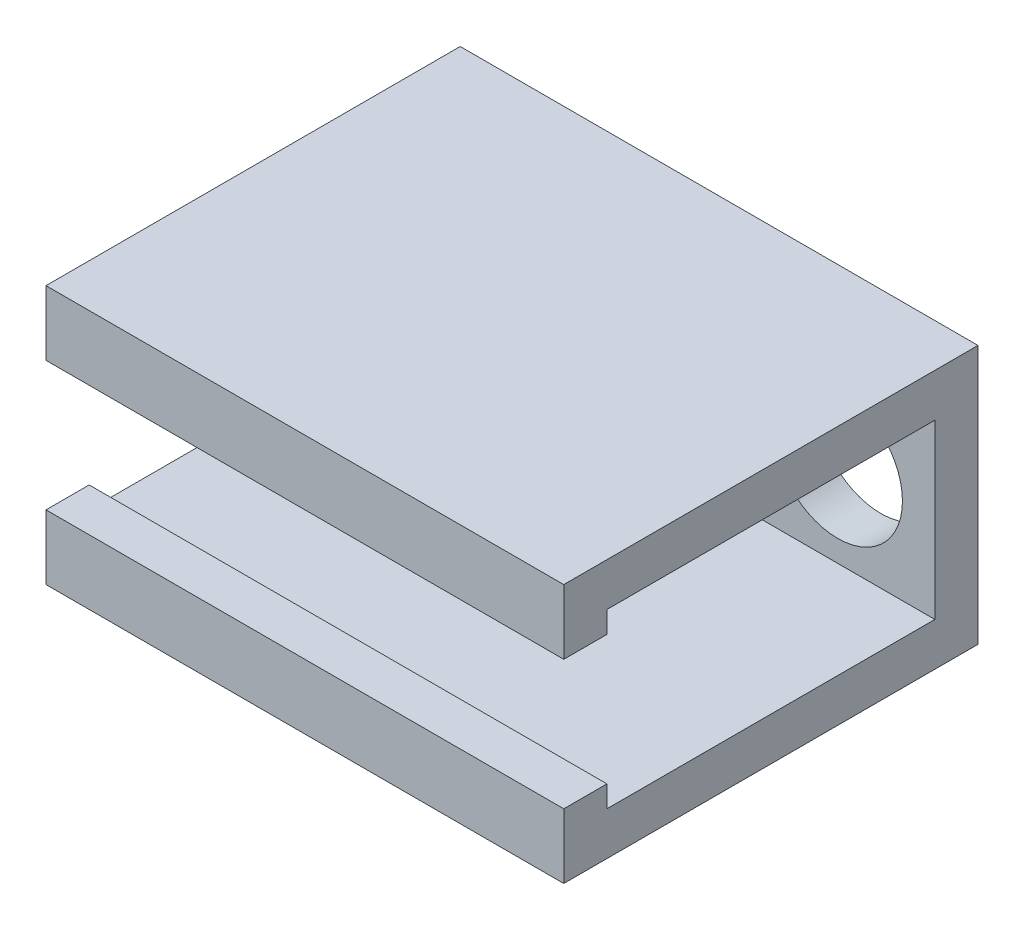
SolidWorks part; units mm, degrees
ref_plane "Front Plane" through (0, 0, 0) normal (0, 0, 1) x (1, 0, 0)
ref_plane "Top Plane" through (0, 0, 0) normal (0, 1, 0) x (1, 0, 0)
ref_plane "Right Plane" through (0, 0, 0) normal (1, 0, 0) x (0, 0, -1)
sketch "Sketch1" plane through (0, 0, 0) normal (1, 0, 0) x (0, 0, -1)
  line L0 (0, 7.5) -> (-5, 7.5)
  line L1 (-5, 7.5) -> (-5, 15)
  line L2 (-5, 15) -> (43, 15)
  line L3 (43, 15) -> (43, -15)
  line L9 (38, -10) -> (38, 10)
  line L11 (0, 7.5) -> (0, 10)
  line L12 (0, 10) -> (38, 10)
  line L13 (43, 0) -> (38, 0)
  line L14 (0, 0) -> (54.5162, 0) construction
  line L15 (-5, -15) -> (43, -15)
  line L16 (-5, -7.5) -> (-5, -15)
  line L17 (0, -7.5) -> (-5, -7.5)
  line L18 (0, -7.5) -> (0, -10)
  line L19 (0, -10) -> (38, -10)
  dimension "D1" = 5
  dimension "D2" = 5
  dimension "D3" = 2.5
  dimension "D4" = 15
  dimension "D5" = 48
extrude "Boss-Extrude1" add sketch "Sketch1" along normal blind 60 contours L13 L3 L2 L1 L0 L11 L12 L9 | L19 L18 L17 L16 L15 L3 L13 L9
sketch "Sketch3" plane through (0, 0, -43) normal (0, 0, -1) x (-1, 0, 0)
  circle A0 centre (-48.7436, 0) radius 7.5
  dimension "D1" = 15
extrude "Cut-Extrude1" cut sketch "Sketch3" against normal through all
